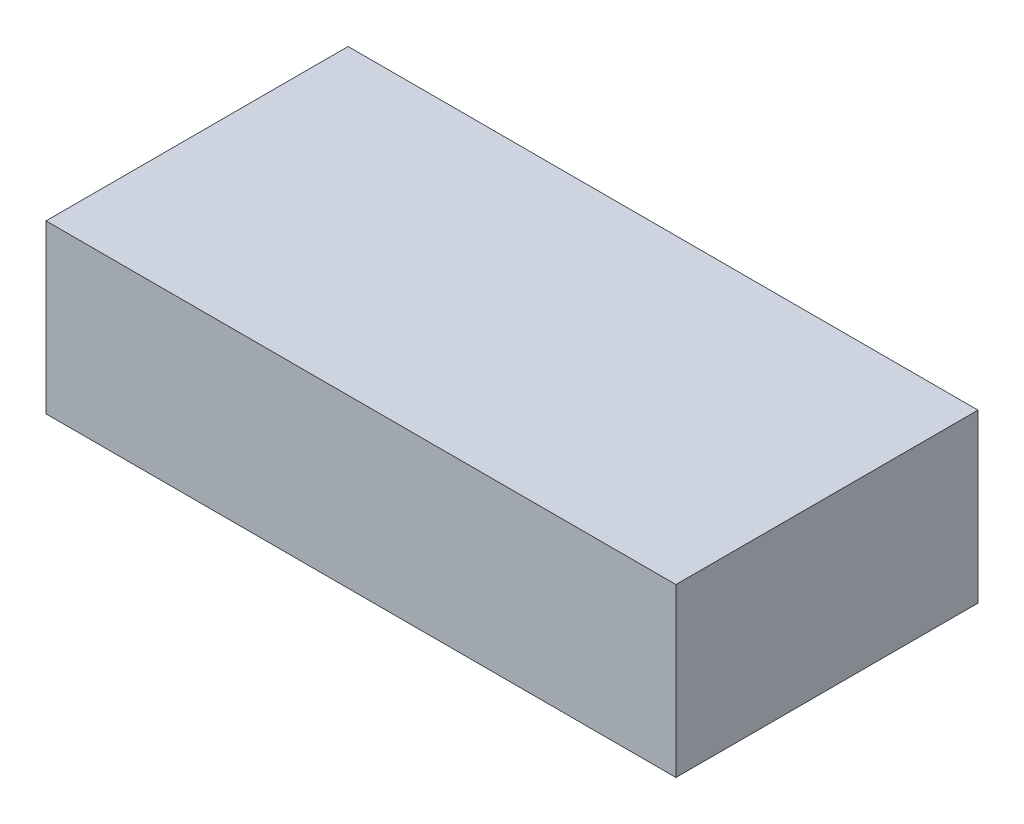
SolidWorks part; units mm, degrees
ref_plane "Front Plane" through (0, 0, 0) normal (0, 0, 1) x (1, 0, 0)
ref_plane "Top Plane" through (0, 0, 0) normal (0, 1, 0) x (1, 0, 0)
ref_plane "Right Plane" through (0, 0, 0) normal (1, 0, 0) x (0, 0, -1)
sketch "Sketch1" plane through (0, 0, 0) normal (0, 1, 0) x (1, 0, 0)
  line L1 (-24.5, -11.75) -> (24.5, -11.75)
  line L2 (-24.5, -11.75) -> (-24.5, 11.75)
  line L3 (-24.5, 11.75) -> (24.5, 11.75)
  line L4 (24.5, -11.75) -> (24.5, 11.75)
  line L5 (-24.5, -11.75) -> (24.5, 11.75) construction
  line L6 (-24.5, 11.75) -> (24.5, -11.75) construction
  point P0 (0, 0)
  dimension "D1" = 49
  dimension "D2" = 23.5
extrude "Boss-Extrude1" add sketch "Sketch1" along normal blind 13
